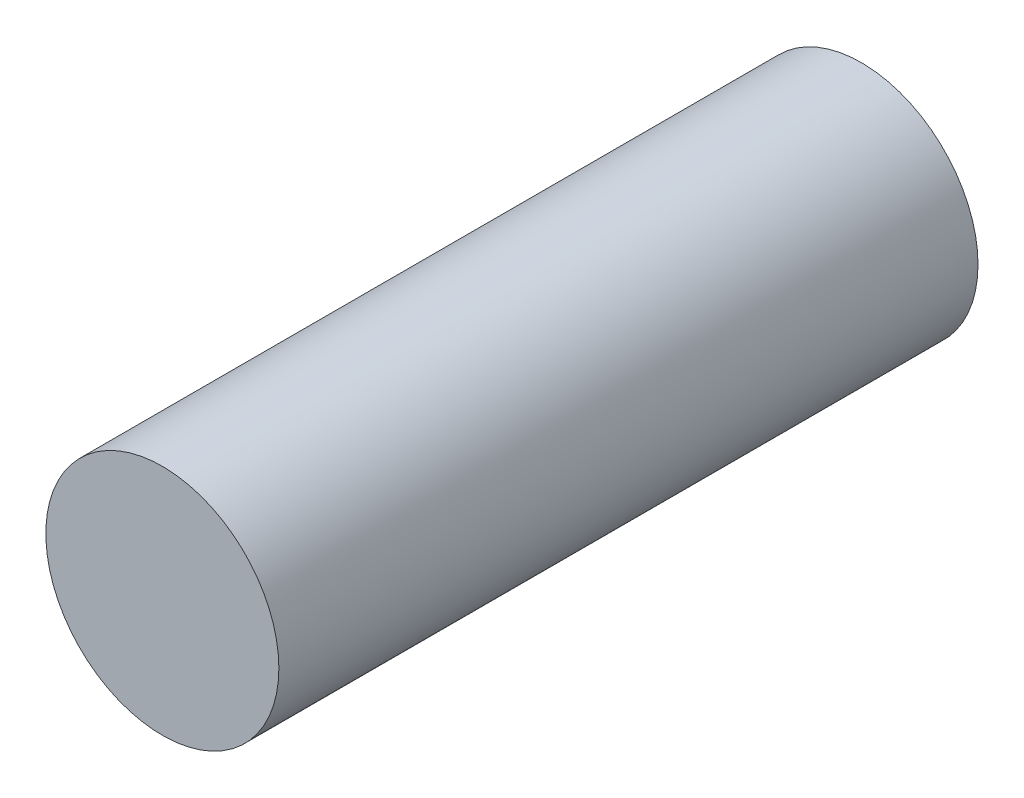
SolidWorks part; units mm, degrees
ref_plane "Front Plane" through (0, 0, 0) normal (0, 0, 1) x (1, 0, 0)
ref_plane "Top Plane" through (0, 0, 0) normal (0, 1, 0) x (1, 0, 0)
ref_plane "Right Plane" through (0, 0, 0) normal (1, 0, 0) x (0, 0, -1)
sketch "Sketch1" plane through (0, 0, 0) normal (0, 0, 1) x (1, 0, 0)
  circle A0 centre (0, 0) radius 5
  dimension "D1" = 10
extrude "Boss-Extrude1" add sketch "Sketch1" along normal blind 30
